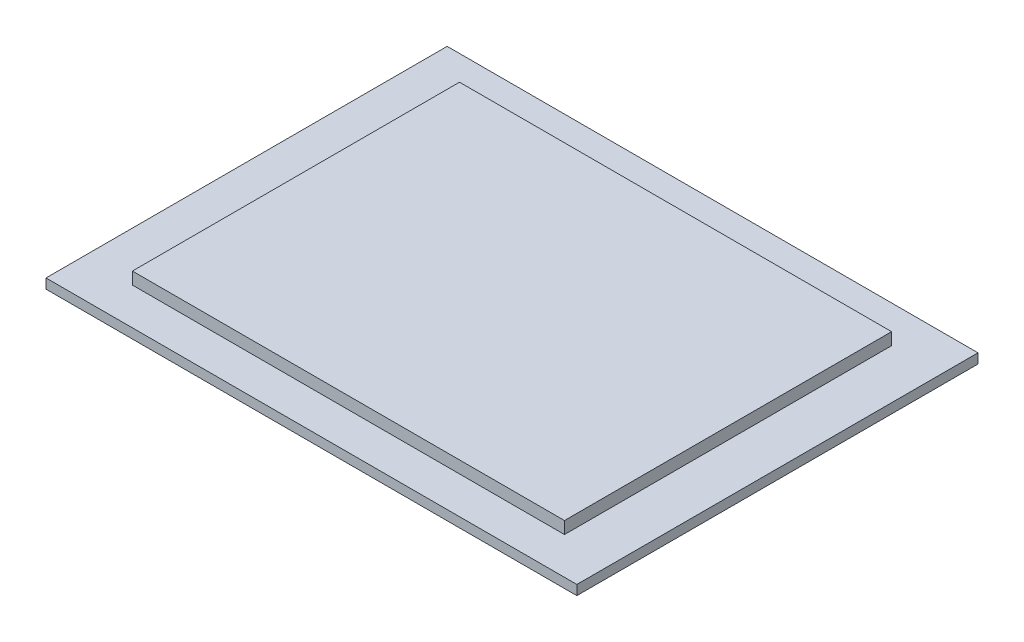
SolidWorks part; units mm, degrees
ref_plane "Front" through (0, 0, 0) normal (0, 0, 1) x (1, 0, 0)
ref_plane "Top" through (0, 0, 0) normal (0, 1, 0) x (1, 0, 0)
ref_plane "Right" through (0, 0, 0) normal (1, 0, 0) x (0, 0, -1)
sketch "Sketch1" plane through (0, 0, 0) normal (0, 1, 0) x (1, 0, 0)
  line L1 (0, 0) -> (42.667, 0)
  line L2 (0, 0) -> (0, -32)
  line L3 (0, -32) -> (42.667, -32)
  line L4 (42.667, 0) -> (42.667, -32)
  dimension "D1" = 42.667
  dimension "D2" = 32
extrude "Extrude1" add sketch "Sketch1" along normal blind 0.3
sketch "Sketch2" plane through (0, 0.3, 0) normal (0, 1, 0) x (-1, 0, 0)
  line L0 (-4.0615, 28.954) -> (0, 32) construction
  line L1 (-4.0615, 3.046) -> (-38.6055, 3.046)
  line L2 (-4.0615, 3.046) -> (-4.0615, 28.954)
  line L3 (-4.0615, 28.954) -> (-38.6055, 28.954)
  line L4 (-38.6055, 3.046) -> (-38.6055, 28.954)
  line L5 (-38.6055, 3.046) -> (-42.667, 0) construction
  dimension "D1" = 34.544
  dimension "D2" = 25.908
extrude "Extrude2" add sketch "Sketch2" along normal blind 1
shell "Shell1" thickness 0.5
